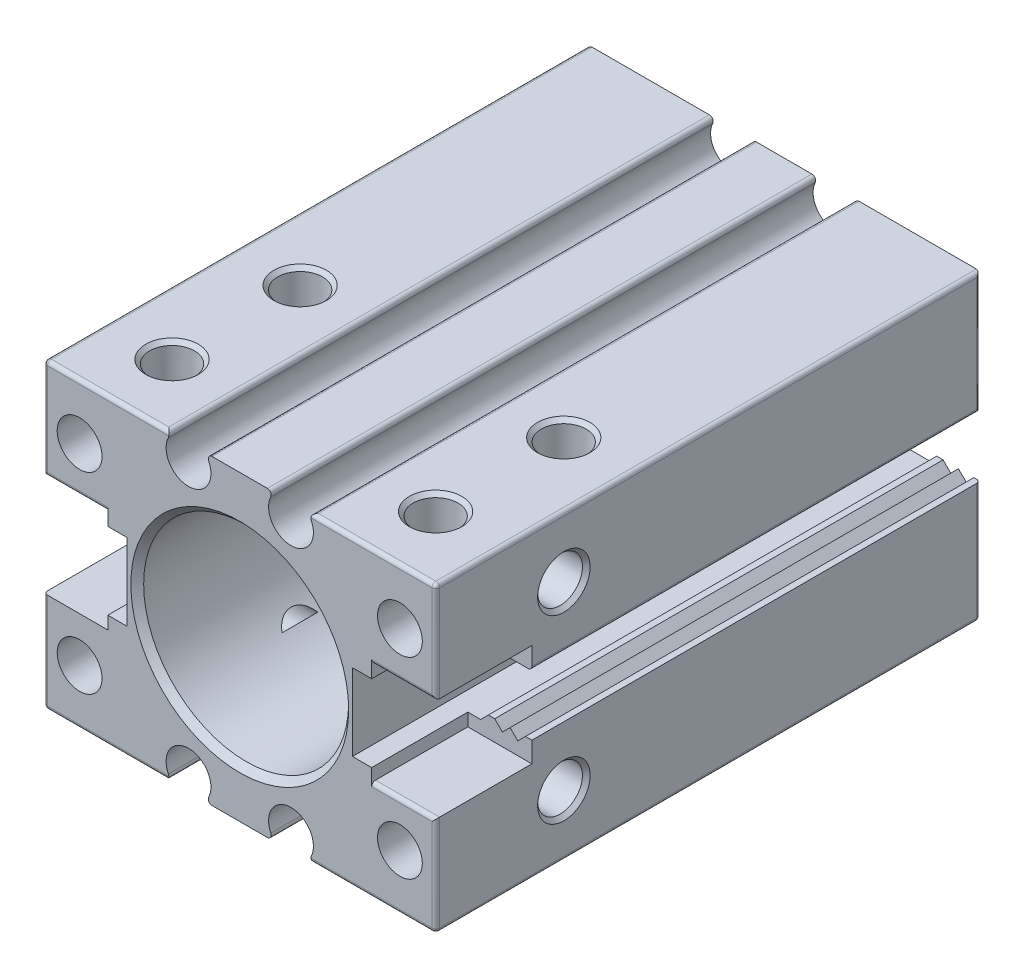
SolidWorks part; units mm, degrees
ref_plane "Front Plane" through (0, 0, 0) normal (0, 0, 1) x (1, 0, 0)
ref_plane "Top Plane" through (0, 0, 0) normal (0, 1, 0) x (1, 0, 0)
ref_plane "Right Plane" through (0, 0, 0) normal (1, 0, 0) x (0, 0, -1)
sketch "Sketch1" plane through (0, 0, 0) normal (0, 0, 1) x (1, 0, 0)
  line L1 (15.3, -11.8) -> (-15.3, -11.8)
  line L2 (15.3, -11.8) -> (15.3, 11.8)
  line L3 (15.3, 11.8) -> (-15.3, 11.8)
  line L4 (-15.3, -11.8) -> (-15.3, 11.8)
  line L5 (15.3, -11.8) -> (-15.3, 11.8) construction
  line L6 (15.3, 11.8) -> (-15.3, -11.8) construction
  point P0 (0, 0)
  dimension "D1" = 30.6
  dimension "D2" = 23.6
extrude "Boss-Extrude1" add sketch "Sketch1" along normal blind 42.5
sketch "Sketch2" plane through (0, 0, 0) normal (0, 0, -1) x (-1, 0, 0)
  line L0 (-15.3, -11.8) -> (-15.3, 11.8) construction
  line L4 (-8.8, -3) -> (-8.8, 3)
  line L5 (-15.3, 0) -> (-8.8, 3) construction
  line L6 (-15.3, 0) -> (-8.8, -3) construction
  line L7 (0, 0) -> (0, 50000) construction
  line L8 (0, 0) -> (-50000, 0) construction
  line L9 (-15.3, -2.4) -> (-15.3, 2.3)
  line L10 (-11.3, -3) -> (-11.9, -2.4)
  line L11 (-11.9, -2.4) -> (-12.4, -2.4)
  line L12 (-12.4, -2.4) -> (-13, -3)
  line L13 (-13, -3) -> (-13.6, -2.4)
  line L14 (-13.6, -2.4) -> (-14.2, -3)
  line L15 (-14.2, -3) -> (-14.8, -2.4)
  line L16 (-14.8, -2.4) -> (-15.3, -2.4)
  line L17 (-8.8, 3) -> (-12.4, 3)
  line L18 (-12.4, 3) -> (-13, 2.3)
  line L19 (-13, 2.3) -> (-15.3, 2.3)
  line L20 (-15.3, 2.3) -> (-15.3, 0)
  line L21 (15.3, 0) -> (8.8, 3) construction
  line L22 (15.3, 2.3) -> (15.3, 0)
  line L23 (13, 2.3) -> (15.3, 2.3)
  line L24 (12.4, 3) -> (13, 2.3)
  line L25 (8.8, 3) -> (12.4, 3)
  line L26 (15.3, -2.3) -> (15.3, 2.3)
  line L27 (8.8, -3) -> (8.8, 3)
  line L28 (15.3, 0) -> (8.8, -3) construction
  line L29 (8.8, -3) -> (12.4, -3)
  line L30 (12.4, -3) -> (13, -2.3)
  line L31 (13, -2.3) -> (15.3, -2.3)
  line L32 (-11.3, -3) -> (-8.8, -3)
  line L33 (15.3, -11.8) -> (-15.3, -11.8) construction
  circle A0 centre (-4, -10.6) radius 1.75
  circle A1 centre (4, -10.6) radius 1.75
  circle A2 centre (4, 10.6) radius 1.75
  circle A3 centre (-4, 10.6) radius 1.75
  point P0 (-15.3, 0)
  dimension "D4" = 3.5
  dimension "D8" = 8
  dimension "D1" = 6.5
  dimension "D2" = 6
  dimension "D3" = 0.5
  dimension "D5" = 4
  dimension "D6" = 2.3
  dimension "D7" = 1.2
  dimension "D9" = 0.6
extrude "Cut-Extrude1" cut sketch "Sketch2" against normal through all both and the other way through all contours L10 L32 L4 L17 L18 L19 L20 L9 L16 L15 L14 L13 L12 L11 | L30 L31 L0 L23 L24 L25 L27 L29 | A3 L18 | L22 A0 | A1 L22 | A2
sketch "Sketch3" plane through (0, 0, 0) normal (0, 0, -1) x (-1, 0, 0)
  circle A0 centre (0, 0) radius 8
  dimension "D1" = 16
extrude "Cut-Extrude2" cut sketch "Sketch3" against normal through all
ref_plane "Plane1" through (0, 0, 5) normal (0, 0, -1) x (-1, 0, 0)
sketch "Sketch4" plane through (0, 0, 5) normal (0, 0, -1) x (-1, 0, 0)
  line L0 (0, 0) -> (-6.9282, 4) construction
  line L1 (-6.9282, 4) -> (0, 0) construction
  line L2 (0, 0) -> (-6.9282, -4) construction
  line L3 (-6.9282, 4) -> (-6.9282, -4) construction
  line L4 (-6.9282, -4) -> (-6.9282, 0) construction
  line L5 (-6.9282, 0) -> (0, 0) construction
  line L6 (-7.5531, 2.6364) -> (-6.3537, 2.336)
  line L7 (-7.5531, -2.6364) -> (-6.3537, -2.336)
  circle A0 centre (0, 0) radius 8 construction
  arc A1 (-7.5531, -2.6364) -> (-7.5531, 2.6364) centre (0, 0) ccw
  arc A2 (-4.9871, -4.9121) -> (-4.9871, 4.9121) centre (0, 0) ccw
  circle A3 centre (-6.0622, 3.5) radius 0.6
  arc A4 (-6.3537, 2.336) -> (-5.0605, 4.1607) centre (-6.0622, 3.5) ccw
  arc A5 (-5.0605, 4.1607) -> (-4.9871, 4.9121) centre (-4.5596, 4.4911) cw
  circle A7 centre (-6.0622, -3.5) radius 0.6
  arc A8 (-6.3537, -2.336) -> (-5.0605, -4.1607) centre (-6.0622, -3.5) cw
  arc A9 (-5.0605, -4.1607) -> (-4.9871, -4.9121) centre (-4.5596, -4.4911) ccw
  circle A10 centre (0, 0) radius 7 construction
  circle A11 centre (0, 0) radius 8 construction
  dimension "D3" = 1.2
  dimension "D4" = 0.6
  dimension "D6" = 0.6
  dimension "D1" = 60
  dimension "D5" = 1.5
  dimension "D2" = 1
extrude "Boss-Extrude2" add sketch "Sketch4" along normal blind 0.5
sketch "Sketch5" plane through (0, 0, 5) normal (0, 0, -1) x (-1, 0, 0)
  circle A0 centre (0, 0) radius 8 construction
  circle A1 centre (0, 0) radius 8
extrude "Boss-Extrude3" add sketch "Sketch5" against normal blind 1
sketch "Sketch7" plane through (0, 0, 0) normal (0, 0, -1) x (-1, 0, 0)
  line L0 (0, 0) -> (0, 50000) construction
  line L1 (15.3, -11.8) -> (-15.3, -11.8) construction
  line L2 (15.3, -11.8) -> (15.3, 11.8) construction
  line L3 (15.3, 11.8) -> (-15.3, 11.8) construction
  line L4 (-15.3, -11.8) -> (-15.3, 11.8) construction
  line L5 (15.3, -11.8) -> (-15.3, 11.8) construction
  line L6 (15.3, 11.8) -> (-15.3, -11.8) construction
  line L7 (12.5, -7.5) -> (-12.5, -7.5) construction
  line L8 (12.5, -7.5) -> (12.5, 7.5) construction
  line L9 (12.5, 7.5) -> (-12.5, 7.5) construction
  line L10 (-12.5, -7.5) -> (-12.5, 7.5) construction
  line L11 (12.5, -7.5) -> (-12.5, 7.5) construction
  line L12 (12.5, 7.5) -> (-12.5, -7.5) construction
  line L13 (0, 0) -> (-50000, 0) construction
  circle A0 centre (-12.5, 7.5) radius 1.75
  circle A1 centre (12.5, 7.5) radius 1.75
  circle A2 centre (12.5, -7.5) radius 1.75
  circle A3 centre (-12.5, -7.5) radius 1.75
  point P0 (0, 0)
  point P13 (0, 0)
  dimension "D2" = 3.5
  dimension "D1" = 25
  dimension "D3" = 15
extrude "Cut-Extrude3" cut sketch "Sketch7" against normal blind 8
sketch "Sketch8" plane through (0, 11.8, 0) normal (0, 1, 0) x (1, 0, 0)
  line L0 (-10.2869, -42.5) -> (-10.2869, 0) construction
  line L1 (-5.2738, -42.5) -> (-15.3, -42.5) construction
  line L2 (-5.2738, 0) -> (-15.3, 0) construction
  line L3 (-10.2869, 0) -> (0, 0) construction
  line L4 (0, 0) -> (0, -42.5) construction
  line L5 (2.7262, -42.5) -> (-2.7262, -42.5) construction
  circle A0 centre (-10.2869, -37.5) radius 1.75
  circle A1 centre (-10.2869, -27.5) radius 1.75
  dimension "D1" = 3.5
  dimension "D2" = 10
  dimension "D3" = 5
extrude "Cut-Extrude4" cut sketch "Sketch8" against normal blind 5
mirror "Mirror1" about plane through (0, 0, 0) normal (0, 1, 0) of "Cut-Extrude4"
sketch "Sketch9" plane through (-15.3, 0, 0) normal (-1, 0, 0) x (0, 0, 1)
  line L0 (0, 0) -> (50000, 0) construction
  line L1 (0, 3) -> (0, -3) construction
  line L2 (42.5, 11.8) -> (42.5, 2.3) construction
  line L3 (35, -4) -> (49.2157, -4)
  line L4 (35, -4) -> (35, 4)
  line L5 (35, 4) -> (49.2157, 4)
  line L6 (49.2157, -4) -> (49.2157, 4)
  line L7 (35, -4) -> (49.2157, 4) construction
  line L8 (35, 4) -> (49.2157, -4) construction
  point P4 (0, 0)
  point P5 (42.1079, 0)
  dimension "D1" = 7.5
  dimension "D2" = 8
extrude "Cut-Extrude5" cut sketch "Sketch9" against normal blind 5
mirror "Mirror2" about plane through (0, 0, 0) normal (1, 0, 0) of "Cut-Extrude5"
sketch "Sketch10" plane through (-15.3, 0, 0) normal (-1, 0, 0) x (0, 0, 1)
  line L0 (0, 7.05) -> (39.2741, 7.05) construction
  line L1 (0, 11.8) -> (0, 2.3) construction
  line L2 (0, 0) -> (50000, 0) construction
  line L3 (42.5, 11.8) -> (42.5, 4) construction
  circle A0 centre (32.5, 7.05) radius 1.75
  circle A1 centre (32.5, -7.05) radius 1.75
  dimension "D1" = 3.5
  dimension "D2" = 10
extrude "Cut-Extrude6" cut sketch "Sketch10" against normal blind 10
chamfer "Chamfer1" distance 0.5 angle 45 2 edges at (-8, 0, 0) (-8, 0, 42.5)
fillet "Fillet1" radius 0.3 35 edges at (12.8, -4, 42.5) (15.3, -7.9, 42.5) (10.2869, -11.8, 42.5) (-10.2869, -11.8, 42.5) (-10.2869, 11.8, 42.5) (-12.8, 4, 42.5) (12.8, 4, 42.5) (15.3, 7.9, 42.5) (10.2869, 11.8, 42.5) (-10.2869, -11.8, 0) (10.2869, -11.8, 0) (15.3, -7.1, 0) (15.3, 7.05, 0) (-15.3, 7.9, 42.5) (-15.3, 7.05, 0) (-15.3, -7.05, 0) (-15.3, -7.9, 42.5) (-13, -2.3, 17.5) (-13, 2.3, 17.5) (13, 2.3, 17.5) (15.3, 2.3, 17.5) (-15.3, 2.3, 17.5) (-15.3, -2.3, 17.5) (-15.3, -11.8, 21.25) (15.3, -11.8, 21.25) (15.3, 11.8, 21.25) (-15.3, 11.8, 21.25) (2.7262, -11.8, 21.25) (5.2738, -11.8, 21.25) (-2.7262, -11.8, 21.25) (-5.2738, -11.8, 21.25) (2.7262, 11.8, 21.25) (5.2738, 11.8, 21.25) (-2.7262, 11.8, 21.25) (-5.2738, 11.8, 21.25)
ref_plane "Plane2" through (0, 0, 21.25) normal (0, 0, 1) x (1, 0, 0)
mirror "Mirror4" about plane through (0, 0, 21.25) normal (0, 0, 1) of "Cut-Extrude3"
mirror "Mirror5" about plane through (0, 0, 0) normal (1, 0, 0) of "Mirror1", "Cut-Extrude4", "Cut-Extrude6"
chamfer "Chamfer2" distance 0.3 angle 45 12 edges at (-15.3, -7.05, 30.75) (-15.3, 7.05, 34.25) (-12.0369, 11.8, 37.5) (-12.0369, 11.8, 27.5) (15.3, -7.05, 30.75) (15.3, 7.05, 34.25) (12.0369, 11.8, 27.5) (12.0369, 11.8, 37.5) (12.0369, -11.8, 27.5) (12.0369, -11.8, 37.5) (-12.0369, -11.8, 37.5) (-12.0369, -11.8, 27.5)
sketch "Sketch12" plane through (0, 0, 0) normal (0, 0, -1) x (-1, 0, 0)
  circle A0 centre (-12.5, 7.5) radius 1.75
  circle A1 centre (12.5, 7.5) radius 1.75
  circle A2 centre (12.5, -7.5) radius 1.75
  circle A3 centre (-12.5, -7.5) radius 1.75
extrude "Boss-Extrude4" add sketch "Sketch12" against normal blind 20
sketch "Sketch13" plane through (0, 0, 0) normal (0, 0, -1) x (-1, 0, 0)
  circle A0 centre (-11, 7.65) radius 2
  circle A1 centre (11, 7.65) radius 2
  circle A2 centre (11, -7.35) radius 2
  circle A3 centre (-11, -7.35) radius 2
extrude "Cut-Extrude7" cut sketch "Sketch13" against normal blind 15
